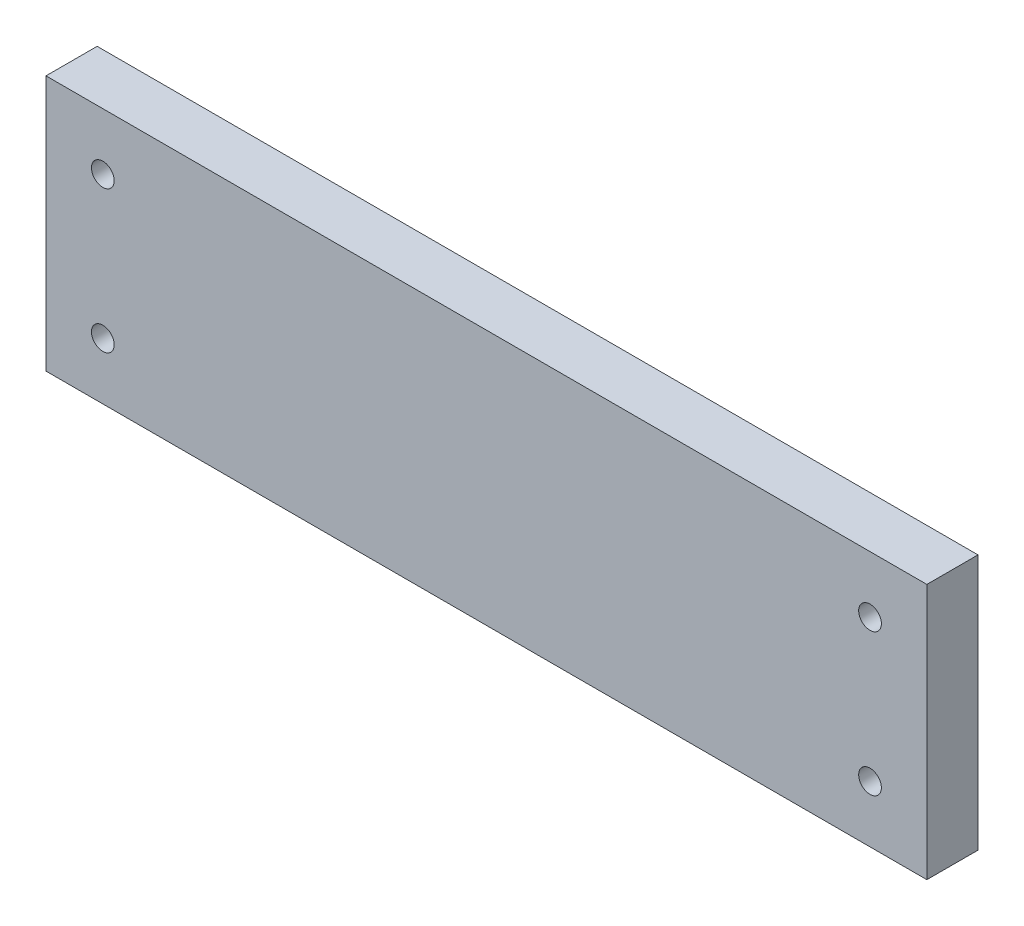
SolidWorks part; units mm, degrees
material "Mahogany"
ref_plane "Front Plane" through (0, 0, 0) normal (0, 0, 1) x (1, 0, 0)
ref_plane "Top Plane" through (0, 0, 0) normal (0, 1, 0) x (1, 0, 0)
ref_plane "Right Plane" through (0, 0, 0) normal (1, 0, 0) x (0, 0, -1)
sketch "Sketch1" plane through (0, 0, 0) normal (0, 0, 1) x (1, 0, 0)
  line L1 (-264.5036, 103.0289) -> (45.4964, 103.0289)
  line L2 (-264.5036, 103.0289) -> (-264.5036, 13.0289)
  line L3 (-264.5036, 13.0289) -> (45.4964, 13.0289)
  line L4 (45.4964, 103.0289) -> (45.4964, 13.0289)
  dimension "D1" = 90
  dimension "D2" = 310
extrude "Boss-Extrude1" add sketch "Sketch1" along normal blind 18
sketch "Sketch2" plane through (0, 0, 18) normal (0, 0, 1) x (1, 0, 0)
  line L0 (-264.5036, 13.0289) -> (45.4964, 13.0289) construction
  line L1 (-264.5036, 103.0289) -> (-264.5036, 13.0289) construction
  line L2 (45.4964, 13.0289) -> (45.4964, 103.0289) construction
  circle A0 centre (-244.5036, 33.0289) radius 4
  circle A1 centre (25.4964, 33.0289) radius 4
  circle A2 centre (25.4964, 83.0289) radius 4
  circle A3 centre (-244.5036, 83.0289) radius 4
  dimension "D1" = 20
  dimension "D2" = 20
  dimension "D3" = 20
  dimension "D4" = 20
  dimension "D5" = 50
  dimension "D6" = 50
  dimension "D7" = 20
  dimension "D8" = 20
extrude "Cut-Extrude1" cut sketch "Sketch2" against normal blind 23 contours A2 | A1 | A0 | A3
